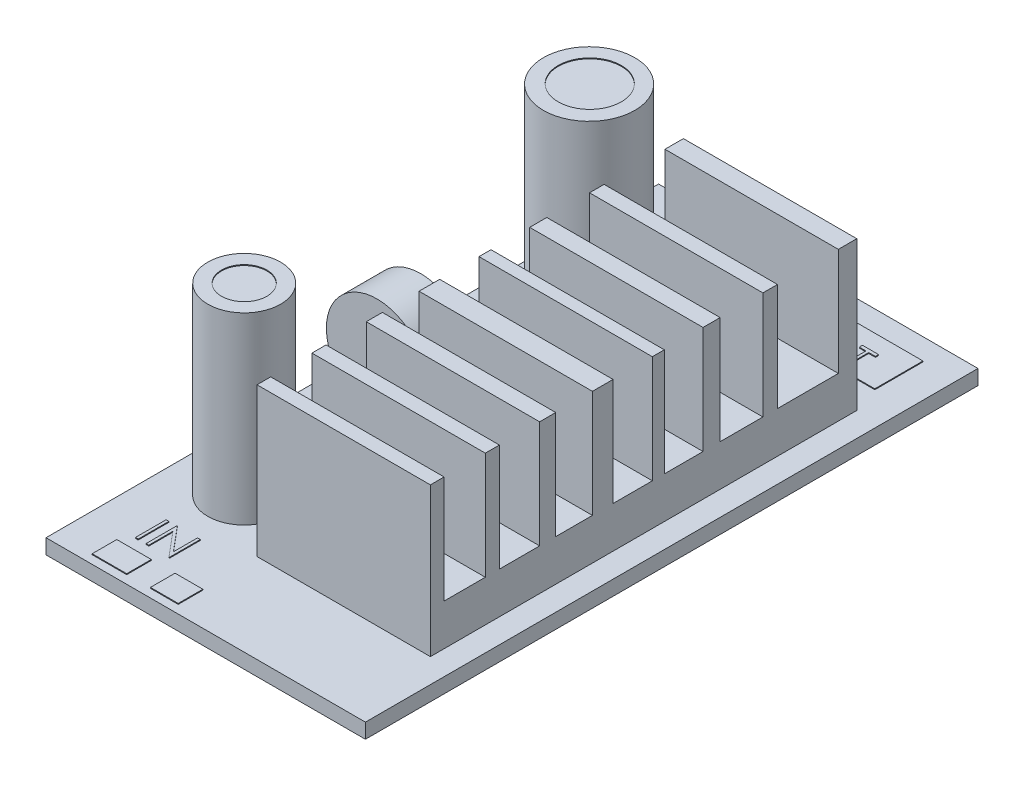
SolidWorks part; units mm, degrees
ref_plane "Front Plane" through (0, 0, 0) normal (0, 0, 1) x (1, 0, 0)
ref_plane "Top Plane" through (0, 0, 0) normal (0, 1, 0) x (1, 0, 0)
ref_plane "Right Plane" through (0, 0, 0) normal (1, 0, 0) x (0, 0, -1)
sketch "Sketch1" plane through (0, 0, 0) normal (0, 1, 0) x (1, 0, 0)
  line L1 (-21.3988, 34.4437) -> (15.1012, 34.4437)
  line L2 (-21.3988, 34.4437) -> (-21.3988, -35.5563)
  line L3 (-21.3988, -35.5563) -> (15.1012, -35.5563)
  line L4 (15.1012, 34.4437) -> (15.1012, -35.5563)
  dimension "D1" = 36.5
  dimension "D2" = 70
extrude "Boss-Extrude1" add sketch "Sketch1" along normal blind 1.7
sketch "Sketch2" plane through (0, 1.7, 0) normal (0, 1, 0) x (1, 0, 0)
  line L1 (-7.4768, 23.3592) -> (12.3339, 23.3592)
  line L2 (-7.4768, 23.3592) -> (-7.4768, -25.3642)
  line L3 (-7.4768, -25.3642) -> (12.3339, -25.3642)
  line L4 (12.3339, 23.3592) -> (12.3339, -25.3642)
extrude "Boss-Extrude2" add sketch "Sketch2" along normal blind 17
sketch "Sketch3" plane through (-7.4768, 0, 0) normal (-1, 0, 0) x (0, 0, 1)
  line L1 (-21.251, 24.2904) -> (-14.2979, 24.2904)
  line L2 (-21.251, 24.2904) -> (-21.251, 6.4194)
  line L3 (-21.251, 6.4194) -> (-14.2979, 6.4194)
  line L4 (-14.2979, 24.2904) -> (-14.2979, 6.4194)
  line L5 (-12.6315, 24.2904) -> (-7.7471, 24.2904)
  line L6 (-12.6315, 24.2904) -> (-12.6315, 6.4194)
  line L7 (-12.6315, 6.4194) -> (-7.7471, 6.4194)
  line L8 (-7.7471, 24.2904) -> (-7.7471, 6.4194)
  line L9 (-5.7933, 24.2904) -> (-1.3687, 24.2904)
  line L10 (-5.7933, 24.2904) -> (-5.7933, 6.4194)
  line L11 (-5.7933, 6.4194) -> (-1.3687, 6.4194)
  line L12 (-1.3687, 24.2904) -> (-1.3687, 6.4194)
  line L13 (0, 24.2904) -> (4.4926, 24.2904)
  line L14 (0, 24.2904) -> (0, 6.4194)
  line L15 (0, 6.4194) -> (4.4926, 6.4194)
  line L16 (4.4926, 24.2904) -> (4.4926, 6.4194)
  line L17 (6.8486, 24.2904) -> (11.0434, 24.2904)
  line L18 (6.8486, 24.2904) -> (6.8486, 6.4194)
  line L19 (6.8486, 6.4194) -> (11.0434, 6.4194)
  line L20 (11.0434, 24.2904) -> (11.0434, 6.4194)
  line L21 (12.8822, 24.2904) -> (17.4793, 24.2904)
  line L22 (12.8822, 24.2904) -> (12.8822, 6.4194)
  line L23 (12.8822, 6.4194) -> (17.4793, 6.4194)
  line L24 (17.4793, 24.2904) -> (17.4793, 6.4194)
  line L25 (19.0882, 24.2904) -> (23.8002, 24.2904)
  line L26 (19.0882, 24.2904) -> (19.0882, 6.4194)
  line L27 (19.0882, 6.4194) -> (23.8002, 6.4194)
  line L28 (23.8002, 24.2904) -> (23.8002, 6.4194)
extrude "Cut-Extrude1" cut sketch "Sketch3" against normal blind 28
sketch "Sketch4" plane through (0, 1.7, 0) normal (0, 1, 0) x (1, 0, 0)
  circle A0 centre (-14.2662, 19.3733) radius 5.2214
  circle A1 centre (-14.2662, -20.0398) radius 4.1644
extrude "Boss-Extrude3" add sketch "Sketch4" along normal blind 21
sketch "Sketch5" plane through (0, 22.7, 0) normal (0, 1, 0) x (1, 0, 0)
  circle A0 centre (-14.2662, 19.4476) radius 3.6072
  circle A1 centre (-14.2662, -20.0398) radius 2.5974
extrude "Cut-Extrude2" cut sketch "Sketch5" against normal blind 0.1
sketch "Sketch6" plane through (0, 1.7, 0) normal (0, 1, 0) x (1, 0, 0)
  line L1 (-17.0745, 32.45) -> (-13.1298, 32.45)
  line L2 (-17.0745, 32.45) -> (-17.0745, 28.3516)
  line L3 (-17.0745, 28.3516) -> (-13.1298, 28.3516)
  line L4 (-13.1298, 32.45) -> (-13.1298, 28.3516)
  line L5 (-10.4146, 32.3475) -> (-6.6749, 32.3475)
  line L6 (-10.4146, 32.3475) -> (-10.4146, 28.2491)
  line L7 (-10.4146, 28.2491) -> (-6.6749, 28.2491)
  line L8 (-6.6749, 32.3475) -> (-6.6749, 28.2491)
  line L9 (-17.0745, -31.7931) -> (-13.1298, -31.7931)
  line L10 (-17.0745, -31.7931) -> (-17.0745, -34.6033)
  line L11 (-17.0745, -34.6033) -> (-13.1298, -34.6033)
  line L12 (-13.1298, -31.7931) -> (-13.1298, -34.6033)
  line L13 (-10.4146, -31.7931) -> (-7.2431, -31.7931)
  line L14 (-10.4146, -31.7931) -> (-10.4146, -34.6033)
  line L15 (-10.4146, -34.6033) -> (-7.2431, -34.6033)
  line L16 (-7.2431, -31.7931) -> (-7.2431, -34.6033)
extrude "Boss-Extrude4" add sketch "Sketch6" along normal blind 0.1
sketch "Sketch7" plane through (0, 1.7, 0) normal (0, 1, 0) x (1, 0, 0)
  text T0 "IN"
  point P1 (-16.6634, -30.5168)
extrude "Boss-Extrude5" add sketch "Sketch7" along normal blind 0.1
sketch "Sketch8" plane through (0, 1.7, 0) normal (0, 1, 0) x (1, 0, 0)
  text T0 "OUT"
  point P1 (-17.1425, 24.5947)
extrude "Boss-Extrude6" add sketch "Sketch8" along normal blind 0.1
sketch "Sketch9" plane through (0, 1.7, 0) normal (0, 1, 0) x (1, 0, 0)
  line L1 (-1.9218, 31.9408) -> (11.3151, 31.9408)
  line L2 (-1.9218, 31.9408) -> (-1.9218, 26.4379)
  line L3 (-1.9218, 26.4379) -> (11.3151, 26.4379)
  line L4 (11.3151, 31.9408) -> (11.3151, 26.4379)
extrude "Boss-Extrude7" add sketch "Sketch9" along normal blind 0.1
sketch "Sketch10" plane through (0, 1.8, 0) normal (0, 1, 0) x (1, 0, 0)
  line L0 (-1.9218, 26.4379) -> (11.3151, 26.4379) construction
  text T0 "POT"
  point P1 (-0.7319, 26.4379)
extrude "Boss-Extrude8" add sketch "Sketch10" along normal blind 0.1
sketch "Sketch11" plane through (0, 0, 0) normal (0, 0, 1) x (1, 0, 0)
  line L0 (-21.3988, 1.7) -> (15.1012, 1.7) construction
  line L1 (-17.1565, 3.8892) -> (-11.3736, 3.8892)
  line L2 (-17.1565, 3.8892) -> (-17.1565, 1.7)
  line L3 (-17.1565, 1.7) -> (-11.3736, 1.7)
  line L4 (-11.3736, 3.8892) -> (-11.3736, 1.7)
  circle A0 centre (-14.1302, 7.9043) radius 5.7854
extrude "Boss-Extrude10" add sketch "Sketch11" along normal blind 5 contours L4 A0 L2 L1 | A0 L2 L3 L4 | L2 A0 L4 L1
